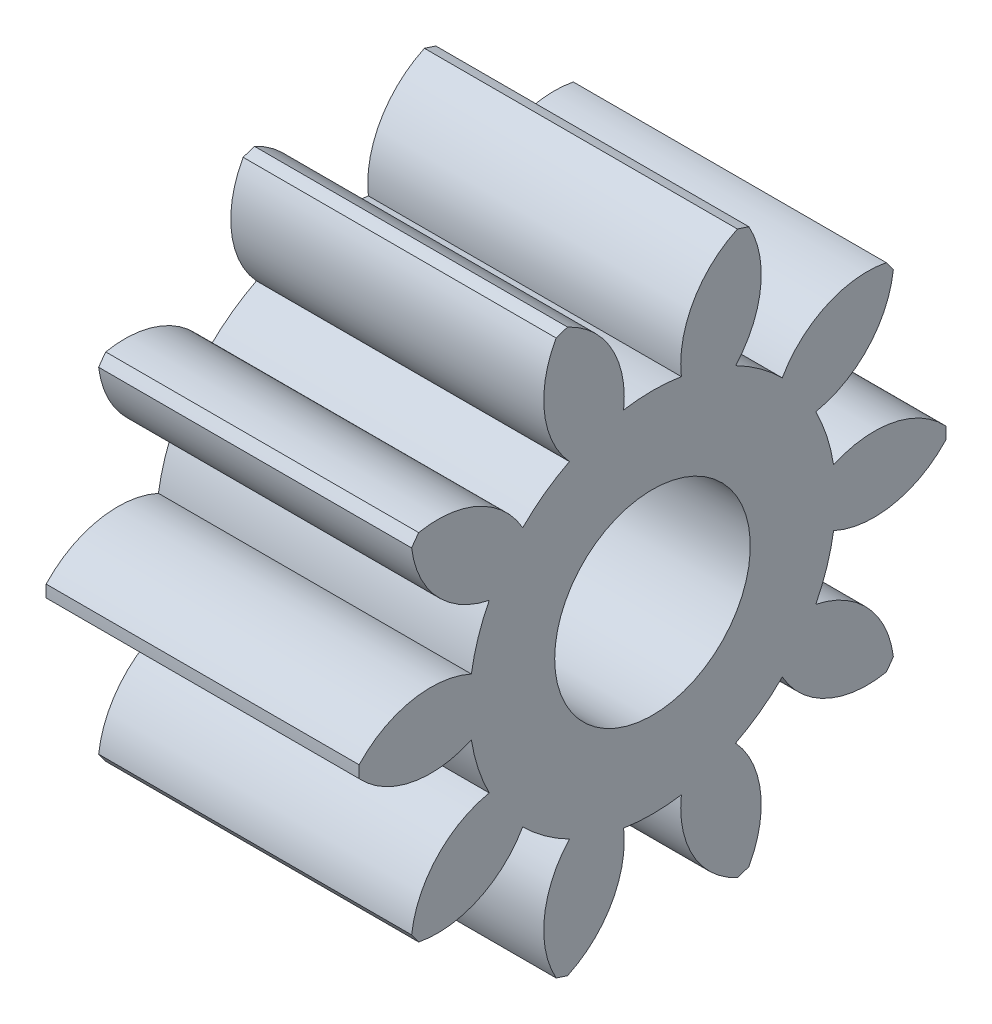
SolidWorks part; units mm, degrees
ref_plane "Plane1" through (0, 0, 0) normal (0, 0, 1) x (1, 0, 0)
ref_plane "Plane2" through (0, 0, 0) normal (0, 1, 0) x (1, 0, 0)
ref_plane "Plane3" through (0, 0, 0) normal (1, 0, 0) x (0, 0, -1)
sketch "HoldingSke" plane through (0, 0, 0) normal (0, 1, 0) x (1, 0, 0)
  line L0 (0, 0) -> (0.7878, -0.1389)
  line L1 (-15, 0) -> (100, 0) construction
  line L2 (0, 0) -> (-2.1039, 2.3779)
  line L3 (0, 0) -> (-11.863, 4.5341)
  line L4 (0, 0) -> (8.5048, 1.4996)
  line L5 (0, 0) -> (-46.8476, -17.4728)
  line L6 (0, 0) -> (-6.6317, -4.4744)
  line L7 (-2.1039, 2.3779) -> (8.6586, 51.2059)
  line L8 (-76.2, 54.61) -> (-75.3, 54.61)
  line L9 (-71.009, 38.7566) -> (-53.1078, 45.2721)
  line L10 (-76.2, 71.12) -> (104.1128, 71.12)
  line L11 (0, 0) -> (-8, 0)
  line L12 (-76.2, 101.6) -> (-76.155, 101.6)
  line L13 (24.9733, 27.94) -> (52.9518, 28.4284)
  line L14 (24.9733, 27.94) -> (24.9743, 27.94)
  line L15 (24.9733, 27.94) -> (100.4006, 29.5858)
  line L16 (-63.627, -1.25) -> (-12.827, -1.25)
  circle A0 centre (0, 0) radius 2.5
  circle A1 centre (0, 0) radius 4.6865
  circle A2 centre (0, 0) radius 37.5
  circle A3 centre (0, 0) radius 2.5
  dimension "MHD" = 9.373
  dimension "Hub_dia" = 75
  dimension "Bore" = 5
  dimension "MBD" = 5
  dimension "Num_teeth" = 10
  dimension "Pitch" = 0.8
  dimension "Overall_len" = 50
  dimension "Show_teeth" = 10
  dimension "Thickness" = 8
  dimension "OAL" = 50.0001
  dimension "T_dim" = 0.9
  dimension "Ap" = 20
  dimension "H" = 19.05
  dimension "Pitch_radius" = 180.3128
  dimension "Width" = 8
  dimension "Backlash" = 0.045
  dimension "Addendum_fac" = 1
  dimension "Dedendum_fac" = 1.25
  dimension "Clearance_fac" = 0.25
  dimension "Dedendum_add" = 0.001
  dimension "Module" = 1.25
sketch "BasProSke" plane through (0, 0, 0) normal (0, 1, 0) x (1, 0, 0)
  line L0 (-10, 0) -> (60, 0) construction
  line L1 (0, 0) -> (0, 7.5)
  line L2 (0, 0) -> (8, 0)
  line L3 (8, 0) -> (8, 7.5)
  line L4 (8, 7.5) -> (0, 7.5)
  dimension "Thickness" = 8
  dimension "Diameter" = 15
revolve "Base-Revolve" add sketch "BasProSke" angle 360 about L0
sketch "TooCutSke" plane through (0, 0, 0) normal (1, 0, 0) x (0, 0, -1)
  line L1 (0, 0) -> (0, 107) construction
  line L2 (0, 0) -> (-1.0563, 6.1601) construction
  line L3 (0, 0) -> (-3.8225, 11.7646) construction
  line L4 (-1.0563, 6.1601) -> (-1.9113, 5.8823) construction
  arc A0 (0.7377, 4.6281) -> (-0.7377, 4.6281) centre (0, 0) ccw
  arc A1 (2.2058, 7.1949) -> (-2.2058, 7.1949) centre (0, 0) ccw
  circle A2 centre (0, 0) radius 6.25 construction
  circle A3 centre (0, 0) radius 5.8731 construction
  arc A4 (-0.7377, 4.6281) -> (-2.2058, 7.1949) centre (-3.2217, 4.9106) ccw
  arc A5 (2.2058, 7.1949) -> (0.7377, 4.6281) centre (3.2217, 4.9106) ccw
  dimension "Root_dia" = 9.373
  dimension "Overcut_dia" = 15.0508
  dimension "Pitch_dia" = 12.5
  dimension "Base_dia" = 11.7462
  dimension "Flank_rad" = 2.5
  dimension "Half_ang" = 18
  dimension "Half_CT" = 0.899
extrude "ToothCut" cut sketch "TooCutSke" along normal through all
fillet "Breaks" [suppressed] radius 0.025
fillet "RootFillets" [suppressed] radius 0.3135
pattern_circular "TeethCuts" count 10 every 36 about axis through (-10, 0, 0) along (1, 0, 0) of "ToothCut", "RootFillets", "Breaks"
sketch "HubNeaOneSke" plane through (0, 0, 0) normal (-1, 0, 0) x (0, 0, 1)
  circle A0 centre (0, 0) radius 4.6865
  dimension "Diameter" = 9.373
extrude "HubNearOne" [suppressed] add sketch "HubNeaOneSke" along normal blind 42.0001
sketch "HubNeaBotSke" plane through (0, 0, 0) normal (-1, 0, 0) x (0, 0, 1)
  circle A0 centre (0, 0) radius 4.6865
  dimension "Diameter" = 9.373
extrude "HubNearBoth" [suppressed] add sketch "HubNeaBotSke" along normal blind 21
ref_plane "FarPln" through (8, 0, 0) normal (1, 0, 0) x (0, 0, -1)
sketch "HubFarSke" plane through (8, 0, 0) normal (1, 0, 0) x (0, 0, -1)
  circle A0 centre (0, 0) radius 4.6865
  dimension "Diameter" = 9.373
extrude "HubFar" [suppressed] add sketch "HubFarSke" along normal blind 21
sketch "BorSke" plane through (0, 0, 0) normal (1, 0, 0) x (0, 0, -1)
  circle A0 centre (0, 0) radius 2.5
  dimension "Diameter" = 5
extrude "Bore" cut sketch "BorSke" along normal mid plane 100.0001
sketch "KeySke" plane through (0, 0, 0) normal (1, 0, 0) x (0, 0, -1)
  line L0 (-1, 0) -> (-1, 3.4)
  line L1 (-1, 3.4) -> (1, 3.4)
  line L2 (1, 3.4) -> (1, 0)
  line L3 (0, 0) -> (0, 34) construction
  line L4 (-1, 0) -> (1, 0)
  dimension "Offset" = 3.4
  dimension "Width" = 2
extrude "Keyway" [suppressed] cut sketch "KeySke" along normal mid plane 100.0001
pattern_circular "Keyway2" [suppressed] count 2 every 90 about axis through (-10, 0, 0) along (1, 0, 0)
equation "' \"Module@HoldingSke\" = 6.35"
equation "' \"Num_teeth@HoldingSke\" = 12"
equation "' \"Ap@HoldingSke\" =  20"
equation "' \"Ap@HoldingSke\" = 20"
equation "' \"Width@HoldingSke\" = 0.5 * 25.4"
equation "' \"Hub_dia@HoldingSke\"= 1 * 25.4"
equation "' \"Hub_dia@HoldingSke\" = 1 * 25.4"
equation "' \"Overall_len@HoldingSke\" = 1.0 * 25.4"
equation "' \"Bore@HoldingSke\" = 0.75 * 25.4"
equation "' \"T_dim@HoldingSke\" = 0.1 * 25.4"
equation "' \"Width@KeySke\" = 0.25 * 25.4"
equation "' \"Show_teeth@HoldingSke\" = 13"
equation "' \"Backlash@HoldingSke\" = 0.009 * 25.4"
equation "' \"Addendum_fac@HoldingSke\" = 1.0"
equation "' \"Dedendum_fac@HoldingSke\" = 1.25"
equation "' \"Dedendum_add@HoldingSke\" = 0.00005 * 25.4"
equation "' \"Clearance_fac@HoldingSke\" = 0.25"
equation "\"Pitch@HoldingSke\" = 1 / \"Module@HoldingSke\""
equation "\"Overcut_dia@TooCutSke\" = (\"Num_teeth@HoldingSke\" + 2 * \"Addendum_fac@HoldingSke\") / \"Pitch@HoldingSke\" + 0.002 * 25.4"
equation "\"Pitch_dia@TooCutSke\" = \"Num_teeth@HoldingSke\" / \"Pitch@HoldingSke\""
equation "\"Base_dia@TooCutSke\" = \"Num_teeth@HoldingSke\" / \"Pitch@HoldingSke\" * cos((\"Ap@HoldingSke\"  * 3.14159265 / 180))"
equation "\"Root_dia@TooCutSke\" = (\"Num_teeth@HoldingSke\" + 2) / \"Pitch@HoldingSke\" - 2 * (\"Addendum_fac@HoldingSke\" + \"Dedendum_fac@HoldingSke\") / \"Pitch@HoldingSke\" - \"Dedendum_add@HoldingSke\" * 2"
equation "\"Half_ang@TooCutSke\" = 180 / \"Num_teeth@HoldingSke\""
equation "\"Half_CT@TooCutSke\" = \"Num_teeth@HoldingSke\" / \"Pitch@HoldingSke\" * sin((3.14159265 / 2 / \"Num_teeth@HoldingSke\")) / 2 - 7 * \"Backlash@HoldingSke\" / 4"
equation "\"Flank_rad@TooCutSke\" = \"Num_teeth@HoldingSke\" / \"Pitch@HoldingSke\" / 5"
equation "\"Radius@RootFillets\" = \"Clearance_fac@HoldingSke\" / \"Pitch@HoldingSke\" + \"Dedendum_add@HoldingSke\""
equation "\"Break_rad@Breaks\" = 0.02 / \"Pitch@HoldingSke\""
equation "\"Thickness@HoldingSke\" = \"Width@HoldingSke\""
equation "\"OAL@HoldingSke\" = \"Thickness@HoldingSke\""
equation "\"MHD@HoldingSke\" = (\"Num_teeth@HoldingSke\" + 2) / \"Pitch@HoldingSke\" - 2 * (\"Addendum_fac@HoldingSke\" + \"Dedendum_fac@HoldingSke\")  / \"Pitch@HoldingSke\" - \"Dedendum_add@HoldingSke\" * 2"
equation "\"MBD@HoldingSke\" = (\"Num_teeth@HoldingSke\" + 2) / \"Pitch@HoldingSke\" - 2 * (\"Addendum_fac@HoldingSke\" + \"Dedendum_fac@HoldingSke\")  / \"Pitch@HoldingSke\" - \"Dedendum_add@HoldingSke\" * 2 - 0.002 * 25.4"
equation "\"MHD@HoldingSke\" = ((sgn( \"MHD@HoldingSke\" - \"Hub_dia@HoldingSke\" )-1)*( \"MHD@HoldingSke\" - \"Hub_dia@HoldingSke\" ))/-2+ \"Hub_dia@HoldingSke\""
equation "\"MBD@HoldingSke\" = ((sgn( \"MBD@HoldingSke\" - \"Bore@HoldingSke\" )-1)*( \"MBD@HoldingSke\" - \"Bore@HoldingSke\" ))/-2+ \"Bore@HoldingSke\""
equation "\"OAL@HoldingSke\" = ((sgn( \"OAL@HoldingSke\" - \"Overall_len@HoldingSke\" )+1)*( \"OAL@HoldingSke\" - \"Overall_len@HoldingSke\" ))/2 + \"Overall_len@HoldingSke\" + 0.000002 * 25.4"
equation "\"Num_teeth@TeethCuts\" = int( \"Show_teeth@HoldingSke\" ) + 1"
equation "\"Num_teeth@TeethCuts\" = ((sgn( \"Num_teeth@TeethCuts\" - \"Num_teeth@HoldingSke\" )-1)*( \"Num_teeth@TeethCuts\" - \"Num_teeth@HoldingSke\" ))/-2+ \"Num_teeth@HoldingSke\""
equation "\"Num_teeth@TeethCuts\" = ((sgn( \"Num_teeth@TeethCuts\" - 2.0)+1)*( \"Num_teeth@TeethCuts\" - 2.0))/2 +2.0"
equation "\"Angle@TeethCuts\" = 360.0 / \"Num_teeth@HoldingSke\""
equation "\"Diameter@BasProSke\" = (\"Num_teeth@HoldingSke\" + 2 * \"Addendum_fac@HoldingSke\") / \"Pitch@HoldingSke\""
equation "\"Thickness@BasProSke\"  = \"Thickness@HoldingSke\""
equation "' \"Fillet_rad@BasProSke\" =  \"Thickness@HoldingSke\" * 0.05"
equation "' \"Fillet_rad@BasProSke\" = \"Thickness@HoldingSke\" * 0.05"
equation "\"MHD@HoldingSke\" = ((sgn( \"MHD@HoldingSke\" - \"Root_dia@TooCutSke\" )-1)*( \"MHD@HoldingSke\" - \"Root_dia@TooCutSke\" ))/-2+ \"Root_dia@TooCutSke\""
equation "\"Diameter@HubNeaOneSke\" = \"MHD@HoldingSke\""
equation "\"Length@HubNearOne\" = \"OAL@HoldingSke\" - \"Thickness@BasProSke\""
equation "\"Diameter@HubNeaBotSke\" = \"MHD@HoldingSke\""
equation "\"Length@HubNearBoth\" = ( \"OAL@HoldingSke\" - \"Thickness@BasProSke\" ) / 2.0"
equation "\"Thickness@FarPln\" = \"Thickness@BasProSke\""
equation "\"Diameter@HubFarSke\" = \"MHD@HoldingSke\""
equation "\"Length@HubFar\" = ( \"OAL@HoldingSke\" - \"Thickness@BasProSke\" ) / 2.0"
equation "\"Diameter@BorSke\" = \"MBD@HoldingSke\""
equation "\"D1@Bore\" = \"OAL@HoldingSke\" * 2.0"
equation "\"D1@Keyway\" = \"OAL@HoldingSke\" * 2.0"
equation "\"Offset@KeySke\" = \"T_dim@HoldingSke\" + \"MBD@HoldingSke\" / 2.0"
